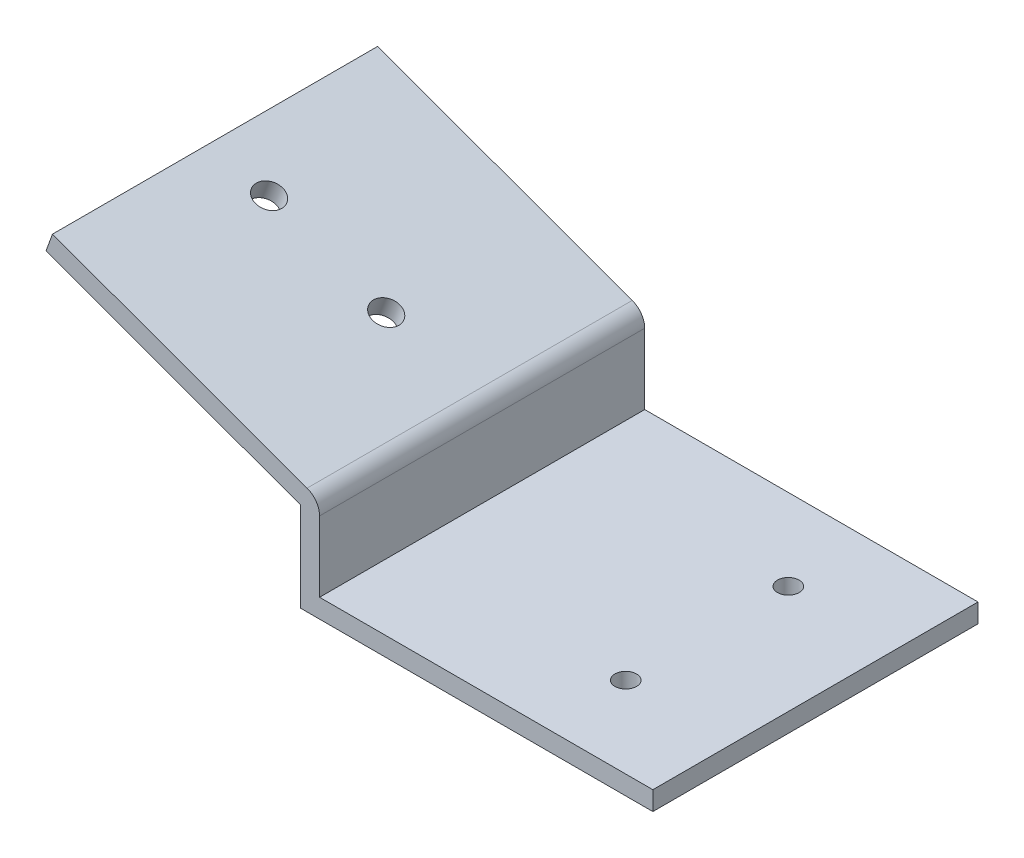
SolidWorks part; units mm, degrees
ref_plane "Front Plane" through (0, 0, 0) normal (0, 0, 1) x (1, 0, 0)
ref_plane "Top Plane" through (0, 0, 0) normal (0, 1, 0) x (1, 0, 0)
ref_plane "Right Plane" through (0, 0, 0) normal (1, 0, 0) x (0, 0, -1)
sketch "Sketch1" plane through (0, 0, 0) normal (0, 1, 0) x (1, 0, 0)
  line L1 (0, 0) -> (65, 0)
  line L2 (0, 0) -> (0, -60)
  line L3 (0, -60) -> (65, -60)
  line L4 (65, 0) -> (65, -60)
  dimension "D1" = 60
  dimension "D2" = 65
extrude "Boss-Extrude1" add sketch "Sketch1" along normal blind 3.5
sketch "Sketch2" plane through (0, 3.5, 0) normal (0, 1, 0) x (1, 0, 0)
  line L0 (0, -60) -> (65, -60) construction
  line L1 (0, 0) -> (3.5, 0)
  line L2 (0, 0) -> (0, -60)
  line L3 (0, -60) -> (3.5, -60)
  line L4 (3.5, 0) -> (3.5, -60)
  dimension "D1" = 3.5
extrude "Boss-Extrude2" add sketch "Sketch2" along normal blind 13
sketch "Sketch7" plane through (0, 0, 60) normal (0, 0, 1) x (1, 0, 0)
  line L0 (0, 16.5) -> (-46.9846, 33.601)
  line L1 (-46.9846, 33.601) -> (-45.7876, 36.8899)
  line L2 (-45.7876, 36.8899) -> (1.1971, 19.7889)
  line L10 (0, 0) -> (65, 0)
  line L11 (65, 0) -> (65, 3.5)
  line L12 (65, 3.5) -> (3.5, 3.5)
  line L13 (3.5, 3.5) -> (3.5, 16.5)
  line L14 (3.5, 16.5) -> (0, 16.5)
  line L15 (0, 16.5) -> (0, 0)
  line L16 (0, 0) -> (65, 0)
  line L17 (65, 0) -> (65, 3.5)
  line L18 (65, 3.5) -> (3.5, 3.5)
  line L19 (3.5, 3.5) -> (3.5, 16.5)
  line L21 (0, 16.5) -> (0, 0)
  arc A0 (1.1971, 19.7889) -> (3.5, 16.5) centre (0, 16.5) cw
  dimension "D1" = 3.5
  dimension "D2" = 50
  dimension "D4" = 110
  dimension "D3" = 0
extrude "Boss-Extrude5" add sketch "Sketch7" against normal blind 60
sketch "Sketch8" plane through (6.5001, 17.8588, 0) normal (0.342, 0.9397, 0) x (0.9397, -0.342, 0)
  circle A0 centre (-44.8392, -30.1812) radius 5
  circle A1 centre (-21.8392, -30.1812) radius 5
  point P4 (-8.8387, -1.6679)
  point P5 (0, 0)
  dimension "D1" = 23
sketch "Sketch9" plane through (0, 3.5, 0) normal (0, 1, 0) x (1, 0, 0)
  line L0 (34.25, 0) -> (34.25, -60) construction
  line L1 (65, 0) -> (3.5, 0) construction
  line L2 (3.5, -60) -> (65, -60) construction
  line L3 (34.25, -30) -> (64.5241, -30) construction
  line L4 (65, -60) -> (65, 0) construction
  circle A0 centre (45, -15) radius 2
  circle A1 centre (45, -45) radius 2
  point P12 (0, 0)
  dimension "D1" = 30
  dimension "D2" = 15
  dimension "D3" = 4
  dimension "D4" = 4
  dimension "D5" = 20
extrude "Cut-Extrude1" cut sketch "Sketch9" against normal blind 60
sketch "Sketch10" plane through (6.5001, 17.8588, 0) normal (0.342, 0.9397, 0) x (0.9397, -0.342, 0)
  circle A0 centre (-44.8392, -30.1812) radius 2.5
  circle A1 centre (-21.8392, -30.1812) radius 2.5
extrude "Cut-Extrude2" cut sketch "Sketch10" against normal blind 60
